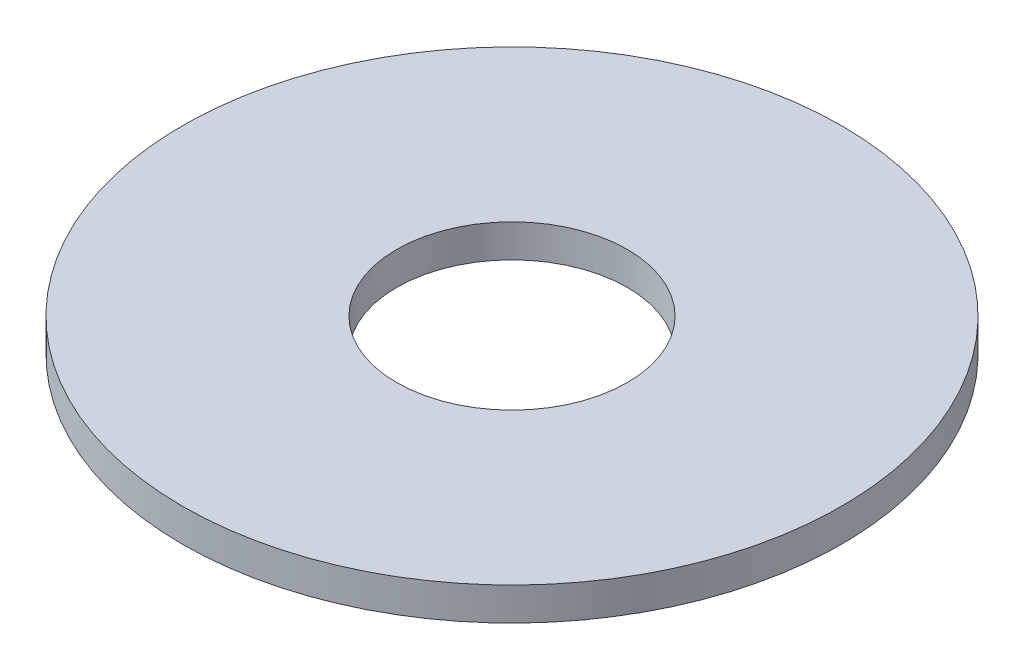
SolidWorks part; units mm, degrees
ref_plane "Front Plane" through (0, 0, 0) normal (0, 0, 1) x (1, 0, 0)
ref_plane "Top Plane" through (0, 0, 0) normal (0, 1, 0) x (1, 0, 0)
ref_plane "Right Plane" through (0, 0, 0) normal (1, 0, 0) x (0, 0, -1)
sketch "Sketch1" plane through (0, 0, 0) normal (0, 1, 0) x (1, 0, 0)
  circle A0 centre (0, 0) radius 50
  circle A1 centre (0, 0) radius 17.5
extrude "Boss-Extrude1" add sketch "Sketch1" along normal blind 5
